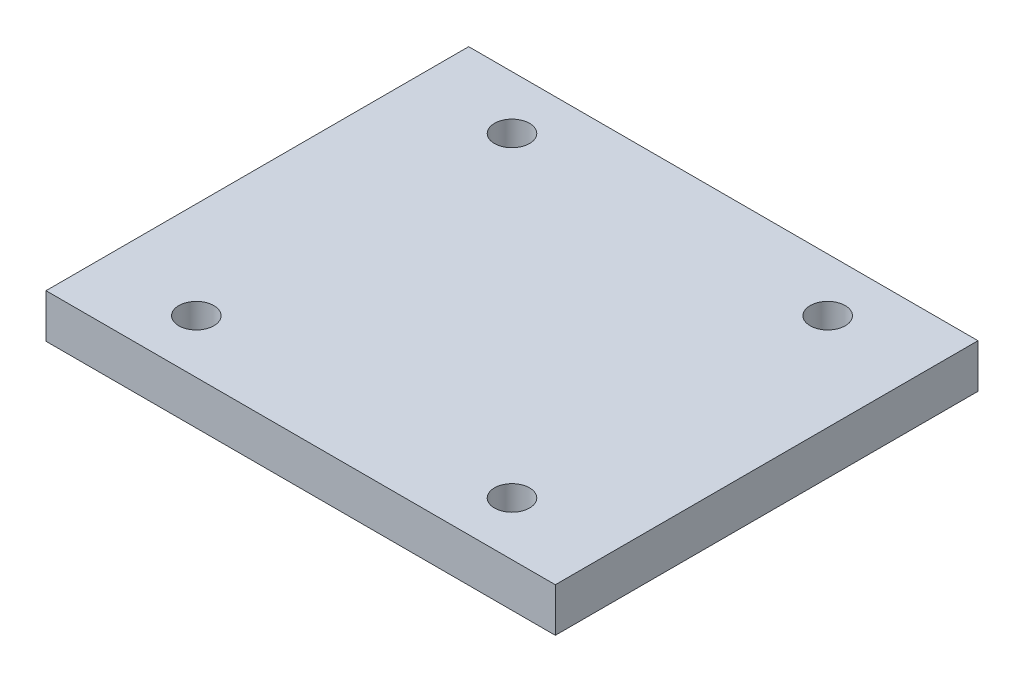
SolidWorks part; units mm, degrees
ref_plane "Front Plane" through (0, 0, 0) normal (0, 0, 1) x (1, 0, 0)
ref_plane "Top Plane" through (0, 0, 0) normal (0, 1, 0) x (1, 0, 0)
ref_plane "Right Plane" through (0, 0, 0) normal (1, 0, 0) x (0, 0, -1)
sketch "Sketch1" plane through (0, 0, 0) normal (0, 1, 0) x (1, 0, 0)
  line L1 (-15.5, -12) -> (13.54, -12)
  line L2 (-15.5, -12) -> (-15.5, 11.1)
  line L3 (-15.5, 11.1) -> (13.54, 11.1)
  line L4 (13.54, -12) -> (13.54, 11.1)
  circle A0 centre (-9.98, 8.55) radius 1
  circle A1 centre (8.02, 8.55) radius 1
  circle A2 centre (8.02, -9.45) radius 1
  circle A3 centre (-9.98, -9.45) radius 1
  point P0 (0, 0)
  point P14 (0, 0)
  dimension "D3" = 2
  dimension "D4" = 2
  dimension "D5" = 2
  dimension "D6" = 2
  dimension "D1" = 23.1
  dimension "D2" = 18
  dimension "D7" = 5.52
  dimension "D8" = 5.52
  dimension "D9" = 5.52
  dimension "D10" = 5.52
  dimension "D11" = 2.55
  dimension "D12" = 2.55
  dimension "D13" = 2.55
  dimension "D14" = 2.55
extrude "Boss-Extrude1" add sketch "Sketch1" along normal blind 2.5
sketch "Sketch2" plane through (0, 0, -11.1) normal (0, 0, -1) x (-1, 0, 0)
  line L4 (-13.54, 0) -> (15.5, 0)
  line L5 (15.5, 0) -> (15.5, 2.5)
  line L6 (15.5, 2.5) -> (-13.54, 2.5)
  line L7 (-13.54, 2.5) -> (-13.54, 0)
  line L8 (-13.54, 0) -> (15.5, 0)
  line L9 (15.5, 0) -> (15.5, 2.5)
  line L10 (15.5, 2.5) -> (-13.54, 2.5)
  line L11 (-13.54, 2.5) -> (-13.54, 0)
  dimension "D1" = 0
extrude "Boss-Extrude2" add sketch "Sketch2" along normal blind 0.5
sketch "Sketch3" plane through (0, 0, 12) normal (0, 0, 1) x (1, 0, 0)
  line L4 (-15.5, 0) -> (13.54, 0)
  line L5 (13.54, 0) -> (13.54, 2.5)
  line L6 (13.54, 2.5) -> (-15.5, 2.5)
  line L7 (-15.5, 2.5) -> (-15.5, 0)
  line L8 (-15.5, 0) -> (13.54, 0)
  line L9 (13.54, 0) -> (13.54, 2.5)
  line L10 (13.54, 2.5) -> (-15.5, 2.5)
  line L11 (-15.5, 2.5) -> (-15.5, 0)
  dimension "D1" = 0
extrude "Boss-Extrude3" add sketch "Sketch3" along normal blind 0.5
